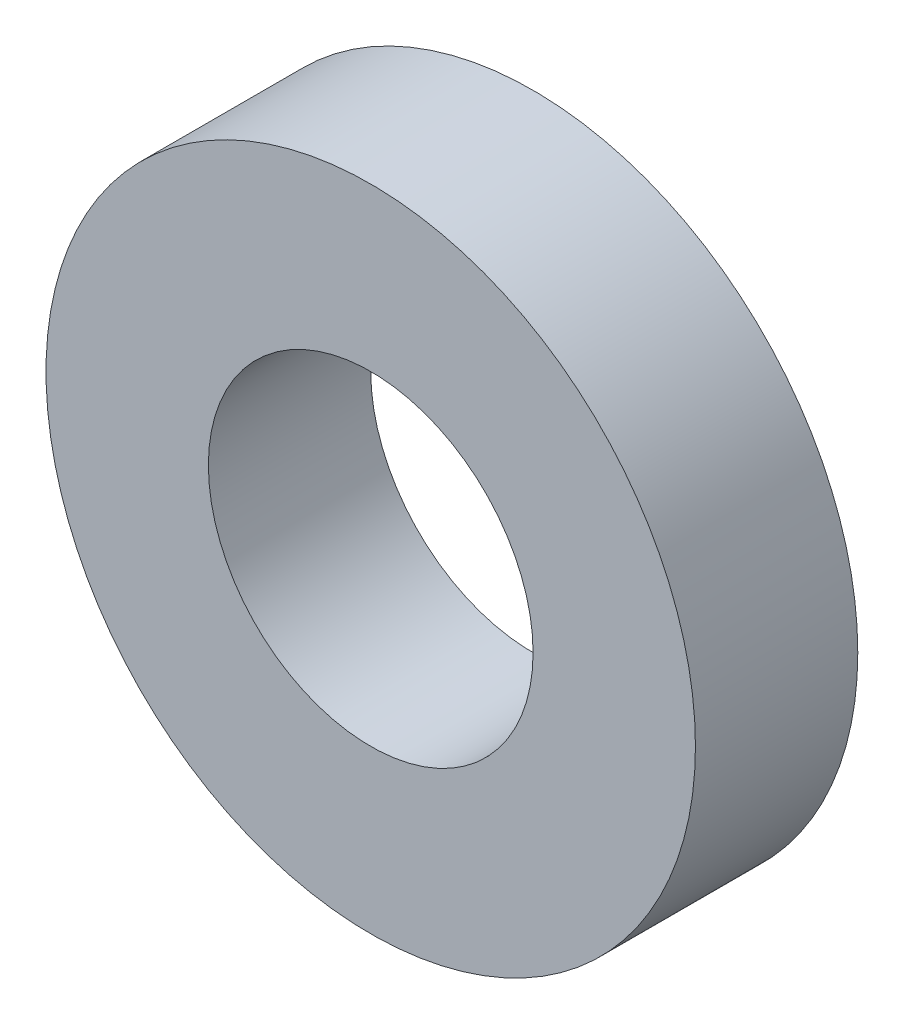
SolidWorks part; units mm, degrees
ref_plane "Front Plane" through (0, 0, 0) normal (0, 0, 1) x (1, 0, 0)
ref_plane "Top Plane" through (0, 0, 0) normal (0, 1, 0) x (1, 0, 0)
ref_plane "Right Plane" through (0, 0, 0) normal (1, 0, 0) x (0, 0, -1)
sketch "Sketch1" plane through (0, 0, 0) normal (0, 0, 1) x (1, 0, 0)
  circle A0 centre (0, 0) radius 3.175
  circle A1 centre (0, 0) radius 6.35
  dimension "D1" = 6.35
  dimension "D2" = 12.7
extrude "Boss-Extrude1" add sketch "Sketch1" along normal blind 3.175
